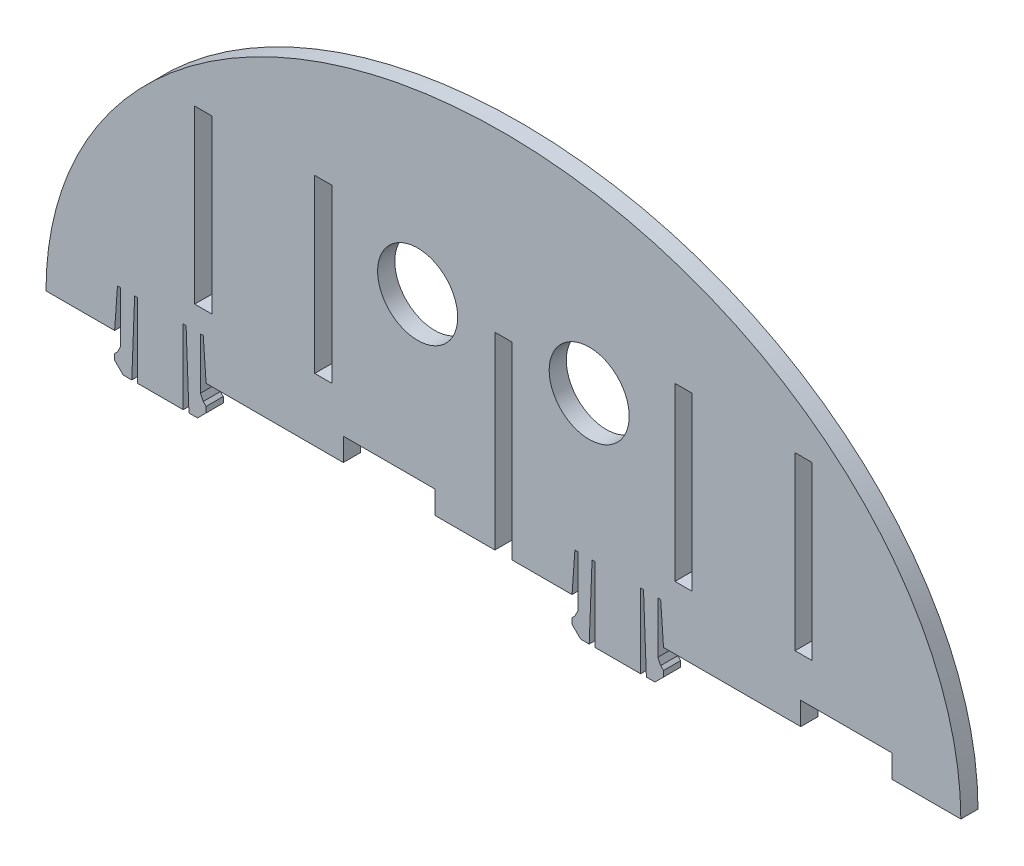
SolidWorks part; units mm, degrees
ref_plane "Front Plane" through (0, 0, 0) normal (0, 0, 1) x (1, 0, 0)
ref_plane "Top Plane" through (0, 0, 0) normal (0, 1, 0) x (1, 0, 0)
ref_plane "Right Plane" through (0, 0, 0) normal (1, 0, 0) x (0, 0, -1)
sketch "Sketch1" plane through (0, 0, 0) normal (0, 0, 1) x (1, 0, 0)
  line L0 (-80, 41.2311) -> (-68, 41.2311)
  line L1 (-52, 41.2311) -> (12, 41.2311)
  line L2 (28, 41.2311) -> (80, 41.2311)
  line L3 (-52, 41.2311) -> (-52.5, 48.2332)
  line L4 (-52.5, 48.2332) -> (-53, 48.2332)
  line L5 (-53, 48.2332) -> (-53, 39.2332)
  line L6 (-53, 39.2332) -> (-52.5, 38.2332)
  line L7 (-52.5, 38.2332) -> (-52, 37.7332)
  line L8 (-52, 37.7332) -> (-52, 36.7332)
  line L9 (-52, 36.7332) -> (-53.5, 35.2332)
  line L10 (-53.5, 35.2332) -> (-55, 35.2332)
  line L11 (-55, 35.2332) -> (-55.5, 48.2332)
  line L12 (-55.5, 48.2332) -> (-56, 48.2332)
  line L13 (-56, 48.2332) -> (-56, 35.2332)
  line L14 (-60, 41.2311) -> (-60, 35.4924) construction
  line L15 (-64, 48.2332) -> (-64, 35.2332)
  line L16 (-64.5, 48.2332) -> (-64, 48.2332)
  line L17 (-65, 35.2332) -> (-64.5, 48.2332)
  line L18 (-66.5, 35.2332) -> (-65, 35.2332)
  line L19 (-68, 36.7332) -> (-66.5, 35.2332)
  line L20 (-68, 37.7332) -> (-68, 36.7332)
  line L21 (-67.5, 38.2332) -> (-68, 37.7332)
  line L22 (-67, 39.2332) -> (-67.5, 38.2332)
  line L23 (-67, 48.2332) -> (-67, 39.2332)
  line L24 (-67.5, 48.2332) -> (-67, 48.2332)
  line L25 (-68, 41.2311) -> (-67.5, 48.2332)
  line L26 (-56, 35.2332) -> (-64, 35.2332)
  line L27 (28, 41.2311) -> (27.5, 48.2332)
  line L28 (27.5, 48.2332) -> (27, 48.2332)
  line L29 (27, 48.2332) -> (27, 39.2332)
  line L30 (27, 39.2332) -> (27.5, 38.2332)
  line L31 (27.5, 38.2332) -> (28, 37.7332)
  line L32 (28, 37.7332) -> (28, 36.7332)
  line L33 (28, 36.7332) -> (26.5, 35.2332)
  line L34 (26.5, 35.2332) -> (25, 35.2332)
  line L35 (25, 35.2332) -> (24.5, 48.2332)
  line L36 (24.5, 48.2332) -> (24, 48.2332)
  line L37 (24, 48.2332) -> (24, 35.2332)
  line L38 (20, 41.2311) -> (20, 35.4924) construction
  line L39 (16, 48.2332) -> (16, 35.2332)
  line L40 (15.5, 48.2332) -> (16, 48.2332)
  line L41 (15, 35.2332) -> (15.5, 48.2332)
  line L42 (13.5, 35.2332) -> (15, 35.2332)
  line L43 (12, 36.7332) -> (13.5, 35.2332)
  line L44 (12, 37.7332) -> (12, 36.7332)
  line L45 (12.5, 38.2332) -> (12, 37.7332)
  line L46 (13, 39.2332) -> (12.5, 38.2332)
  line L47 (13, 48.2332) -> (13, 39.2332)
  line L48 (12.5, 48.2332) -> (13, 48.2332)
  line L49 (12, 41.2311) -> (12.5, 48.2332)
  line L50 (24, 35.2332) -> (16, 35.2332)
  line L51 (-80, 41.2311) -> (0, 0) construction
  line L52 (0, 0) -> (80, 41.2311) construction
  line L53 (80, 41.2311) -> (80.095, 41.7661) construction
  ellipse E0 centre (0, 41.2311) end of major axis (-80, 41.2311) minor radius 63.9989 (0, 105.23) -> (-80, 41.2311) ccw
  ellipse E1 centre (0, 41.2311) end of major axis (80, 41.2311) minor radius 63.9989 (0, 105.23) -> (80, 41.2311) cw
  point P10 (-60, 41.2311)
  point P11 (-52, 41.2311)
  point P12 (-68, 41.2311)
  point P13 (-68, 41.2311)
  point P38 (20, 41.2311)
  point P39 (28, 41.2311)
  point P40 (12, 41.2311)
  point P41 (12, 41.2311)
  dimension "D1" = 52
  dimension "D2" = 64
  dimension "D3" = 12
  dimension "D4" = 8
  dimension "D5" = 0.5
  dimension "D6" = 9
  dimension "D7" = 0.5
  dimension "D8" = 1
  dimension "D9" = 0.5
  dimension "D10" = 0.5
  dimension "D11" = 1
  dimension "D12" = 1.5
  dimension "D13" = 1.5
  dimension "D14" = 0.5
  dimension "D15" = 0.5
  dimension "D16" = 13
  dimension "D17" = 7.0022
  dimension "D18" = 0.5
  dimension "D19" = 1.5
  dimension "D20" = 13
  dimension "D21" = 8
  dimension "D22" = 8
  dimension "D23" = 0.5
  dimension "D24" = 9
  dimension "D25" = 0.5
  dimension "D26" = 1
  dimension "D27" = 0.5
  dimension "D28" = 0.5
  dimension "D29" = 1
  dimension "D30" = 1.5
  dimension "D31" = 1.5
  dimension "D32" = 0.5
  dimension "D33" = 0.5
  dimension "D34" = 13
  dimension "D35" = 7.0022
  dimension "D36" = 0.5
  dimension "D37" = 1.5
  dimension "D38" = 13
  dimension "D39" = 8
  dimension "D40" = 63.9989
  dimension "D41" = 90
  dimension "D42" = 90
  dimension "D43" = 80
  dimension "D44" = 41.2311
extrude "Boss-Extrude1" add sketch "Sketch1" along normal blind 3
sketch "Sketch3" plane through (0, 0, 3) normal (0, 0, 1) x (1, 0, 0)
  line L0 (-1.5, 41.2311) -> (-1.5, 74.2311)
  line L1 (-52, 41.2311) -> (12, 41.2311) construction
  line L2 (1.5, 41.2311) -> (1.5, 74.2311)
  line L3 (-1.5, 74.2311) -> (1.5, 74.2311)
  dimension "D1" = 3
  dimension "D2" = 33
  dimension "D3" = 50.5
extrude "Cut-Extrude1" cut sketch "Sketch3" against normal blind 3 and the other way through all
sketch "Sketch4" plane through (0, 0, 3) normal (0, 0, 1) x (1, 0, 0)
  line L0 (-28, 41.2311) -> (-28, 45.2311)
  line L1 (-52, 41.2311) -> (-1.5, 41.2311) construction
  line L2 (-28, 45.2311) -> (-12, 45.2311)
  line L3 (-12, 45.2311) -> (-12, 41.2311)
  dimension "D1" = 4
  dimension "D2" = 16
  dimension "D3" = 24
extrude "Cut-Extrude2" cut sketch "Sketch4" against normal blind 3 and the other way through all flip side to cut
sketch "Sketch5" plane through (0, 0, 3) normal (0, 0, 1) x (1, 0, 0)
  line L0 (68, 41.2311) -> (68, 45.2311)
  line L1 (28, 41.2311) -> (80, 41.2311) construction
  line L2 (68, 45.2311) -> (52, 45.2311)
  line L3 (52, 45.2311) -> (52, 41.2311)
  dimension "D1" = 16
  dimension "D2" = 4
  dimension "D3" = 12
extrude "Cut-Extrude3" cut sketch "Sketch5" against normal blind 3 and the other way through all
sketch "Sketch7" plane through (0, 0, 3) normal (0, 0, 1) x (1, 0, 0)
  line L0 (0, 41.2311) -> (0, 105.23) construction
  line L1 (-51, 82.231) -> (-51, 52.231)
  line L2 (51, 82.231) -> (51, 52.231)
  line L3 (-51, 82.231) -> (-54, 82.231)
  line L4 (51, 82.231) -> (54, 82.231)
  line L5 (-51, 52.231) -> (-54, 52.231)
  line L6 (51, 52.231) -> (54, 52.231)
  line L7 (-54, 52.231) -> (-54, 82.231)
  line L8 (54, 52.231) -> (54, 82.231)
  line L9 (-30, 82.231) -> (-30, 52.231)
  line L10 (30, 82.231) -> (30, 52.231)
  line L11 (-30, 82.231) -> (-33, 82.231)
  line L12 (30, 82.231) -> (33, 82.231)
  line L13 (-30, 52.231) -> (-33, 52.231)
  line L14 (30, 52.231) -> (33, 52.231)
  line L15 (-33, 82.231) -> (-33, 52.231)
  line L16 (33, 82.231) -> (33, 52.231)
  dimension "D1" = 30
  dimension "D2" = 3
  dimension "D3" = 51
  dimension "D4" = 52.231
  dimension "D5" = 30
  dimension "D6" = 3
  dimension "D7" = 30
  dimension "D8" = 52.231
  dimension "D9" = 33
  dimension "D10" = 3
extrude "Cut-Extrude4" cut sketch "Sketch7" against normal blind 3
sketch "Sketch8" plane through (0, 0, 3) normal (0, 0, 1) x (1, 0, 0)
  line L2 (0, 74.2311) -> (0, 105.23) construction
  line L3 (-1.5, 74.2311) -> (1.5, 74.2311) construction
  circle A0 centre (-15, 73.23) radius 7
  circle A1 centre (15, 73.23) radius 7
  ellipse E0 centre (0, 41.2311) end of major axis (-80, 41.2311) minor radius 63.9989 (0, 105.23) -> (-80, 41.2311) ccw construction
  dimension "D1" = 14
  dimension "D2" = 15
  dimension "D3" = 73.23
extrude "Cut-Extrude5" cut sketch "Sketch8" against normal blind 3
sketch "Sketch9" plane through (0, 0, 3) normal (0, 0, 1) x (1, 0, 0)
  text T0 "HY3a" font "Century Gothic" height in points 22
  dimension "D1" = 26
  dimension "D2" = 9
